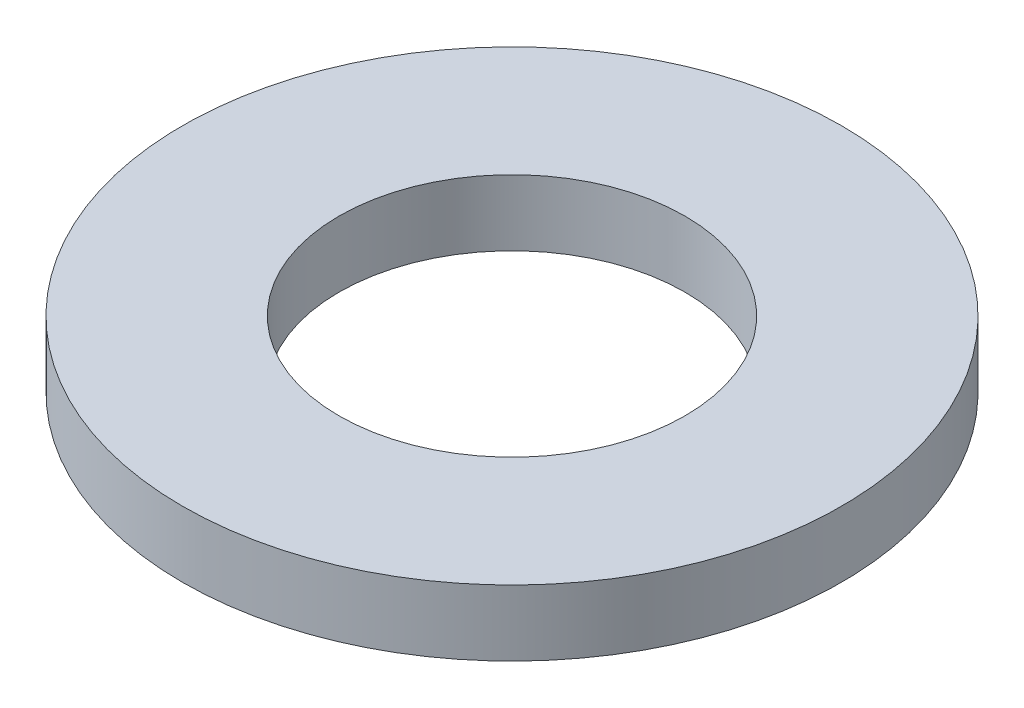
SolidWorks part; units mm, degrees
material "Plain Carbon Steel"
ref_plane "Front Plane" through (0, 0, 0) normal (0, 0, 1) x (1, 0, 0)
ref_plane "Top Plane" through (0, 0, 0) normal (0, 1, 0) x (1, 0, 0)
ref_plane "Right Plane" through (0, 0, 0) normal (1, 0, 0) x (0, 0, -1)
sketch "Sketch1" plane through (0, 0, 0) normal (0, 1, 0) x (1, 0, 0)
  circle A0 centre (0, 0) radius 5.25
  circle A1 centre (0, 0) radius 10
  dimension "D1" = 10.5
  dimension "D2" = 20
extrude "Extrude1" add sketch "Sketch1" along normal blind 2
